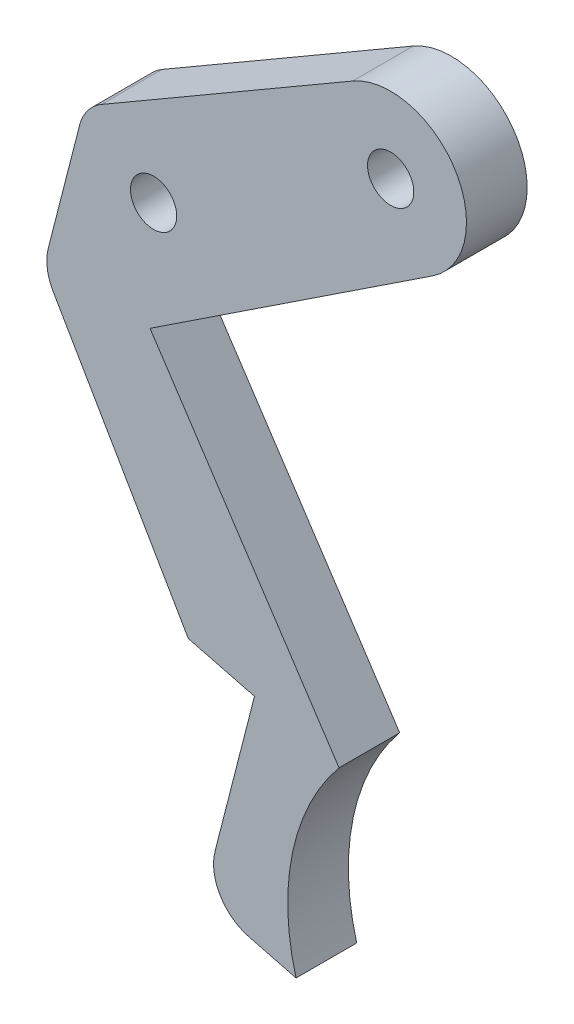
SolidWorks part; units mm, degrees
ref_plane "Alzado" through (0, 0, 0) normal (0, 0, 1) x (1, 0, 0)
ref_plane "Planta" through (0, 0, 0) normal (0, 1, 0) x (1, 0, 0)
ref_plane "Vista lateral" through (0, 0, 0) normal (1, 0, 0) x (0, 0, -1)
sketch "Croquis2" plane through (0, 0, 0) normal (0, 0, 1) x (1, 0, 0)
  line L0 (-51.2799, -17.9947) -> (-56.4417, -38.1257)
  line L1 (6.8903, -10.4295) -> (-39.671, -41.1903)
  line L2 (-55.6399, -43.9269) -> (-33.3681, -82.3178)
  line L3 (-47.6725, -13.2281) -> (-6.277, 10.8097)
  line L4 (-33.3681, -82.3178) -> (-22.4492, -85.1175)
  line L5 (-15.597, -121.9043) -> (-23.3864, -119.907)
  line L6 (-28.9564, -110.4957) -> (-22.4492, -85.1175)
  line L7 (-39.671, -41.1903) -> (-8.5116, -88.3548)
  arc A0 (6.8903, -10.4295) -> (-6.277, 10.8097) centre (0, 0) ccw
  arc A1 (-15.597, -121.9043) -> (-8.5116, -88.3548) centre (20.0111, -111.9015) cw
  arc A2 (-23.3864, -119.907) -> (-28.9564, -110.4957) centre (-21.4657, -112.4163) cw
  arc A3 (-56.4417, -38.1257) -> (-55.6399, -43.9269) centre (-48.951, -40.0464) ccw
  arc A4 (-47.6725, -13.2281) -> (-51.2799, -17.9947) centre (-43.7892, -19.9154) ccw
  dimension "D1" = 25
  dimension "D2" = 7.733
extrude "Saliente-Extruir1" add sketch "Croquis2" along normal blind 10
sketch "Croquis4" plane through (0, 0, 0) normal (0, 0, 1) x (1, 0, 0)
  line L0 (0, 0) -> (-39.0801, -22.9723) construction
  circle A0 centre (0, 0) radius 3.81
  circle A1 centre (-39.0801, -22.9723) radius 3.81
  dimension "D1" = 7.62
  dimension "D2" = 7.62
extrude "Cortar-Extruir1" cut sketch "Croquis4" along normal blind 61.468 and the other way blind 64.008
